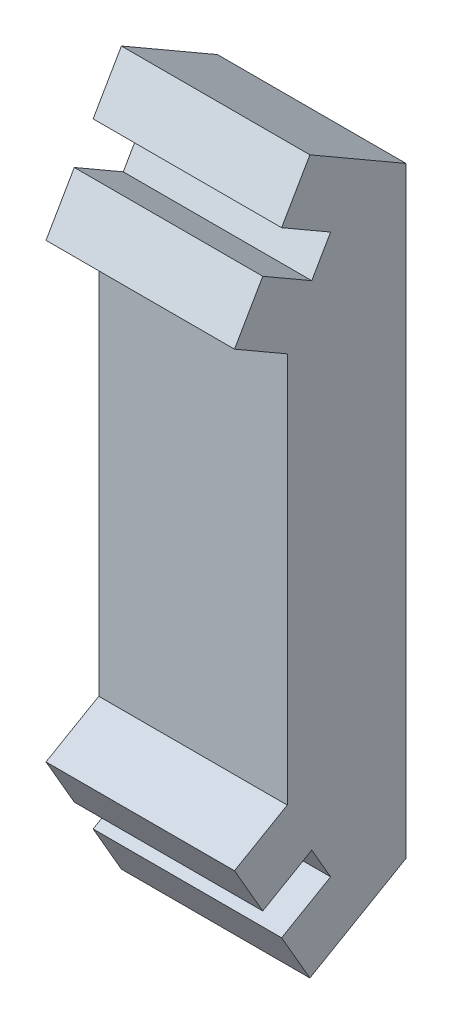
SolidWorks part; units mm, degrees
ref_plane "Спереди" through (0, 0, 0) normal (0, 0, 1) x (1, 0, 0)
ref_plane "Сверху" through (0, 0, 0) normal (0, 1, 0) x (1, 0, 0)
ref_plane "Справа" through (0, 0, 0) normal (1, 0, 0) x (0, 0, -1)
sketch "Эскиз1" plane through (0, 0, 0) normal (1, 0, 0) x (0, 0, -1)
  line L0 (-2.0398, 21.0469) -> (-2.0398, -5.1131) construction
  line L1 (-2.0398, 21.0469) -> (-4.6379, 22.5469)
  line L3 (-3.3389, 21.7969) -> (-2.3389, 23.5289) construction
  line L4 (-3.3389, -5.8631) -> (-2.3389, -7.5952) construction
  line L5 (-2.3389, 23.5289) -> (-1.0398, 22.7789)
  line L7 (-1.0398, 22.7789) -> (-1.0398, -6.8452) construction
  line L8 (-2.0398, 21.0469) -> (-1.0398, 22.7789)
  line L10 (-4.6379, 22.5469) -> (-6.1379, 19.9488)
  line L12 (-6.1379, 19.9488) -> (-3.3389, 18.3328)
  line L14 (-3.3389, -2.399) -> (-3.3389, 18.3328)
  line L15 (-2.3389, 23.5289) -> (-3.6379, 24.2789)
  line L17 (-3.6379, 24.2789) -> (-2.1379, 26.877)
  line L18 (-2.1379, 26.877) -> (2.9602, 23.9336)
  line L21 (2.9602, -7.9999) -> (2.9602, 23.9336)
  line L22 (-3.3389, 7.9669) -> (2.9602, 7.9669) construction
  line L23 (-2.1379, -10.9432) -> (2.9602, -7.9999)
  line L24 (-3.6379, -8.3452) -> (-2.1379, -10.9432)
  line L25 (-2.3389, -7.5952) -> (-3.6379, -8.3452)
  line L26 (-6.1379, -4.015) -> (-3.3389, -2.399)
  line L27 (-4.6379, -6.6131) -> (-6.1379, -4.015)
  line L28 (-2.0398, -5.1131) -> (-1.0398, -6.8452)
  line L29 (-2.3389, -7.5952) -> (-1.0398, -6.8452)
  line L30 (-2.0398, -5.1131) -> (-4.6379, -6.6131)
  point P7 (-1.0398, 7.9669)
  point P12 (-2.0398, 7.9669)
  dimension "D1" = 3
  dimension "D2" = 13.08
  dimension "D3" = 4
  dimension "D5" = 60
  dimension "D7" = 2
  dimension "D8" = 3
  dimension "D9" = 3
extrude "Бобышка-Вытянуть1" add sketch "Эскиз1" along normal blind 10
